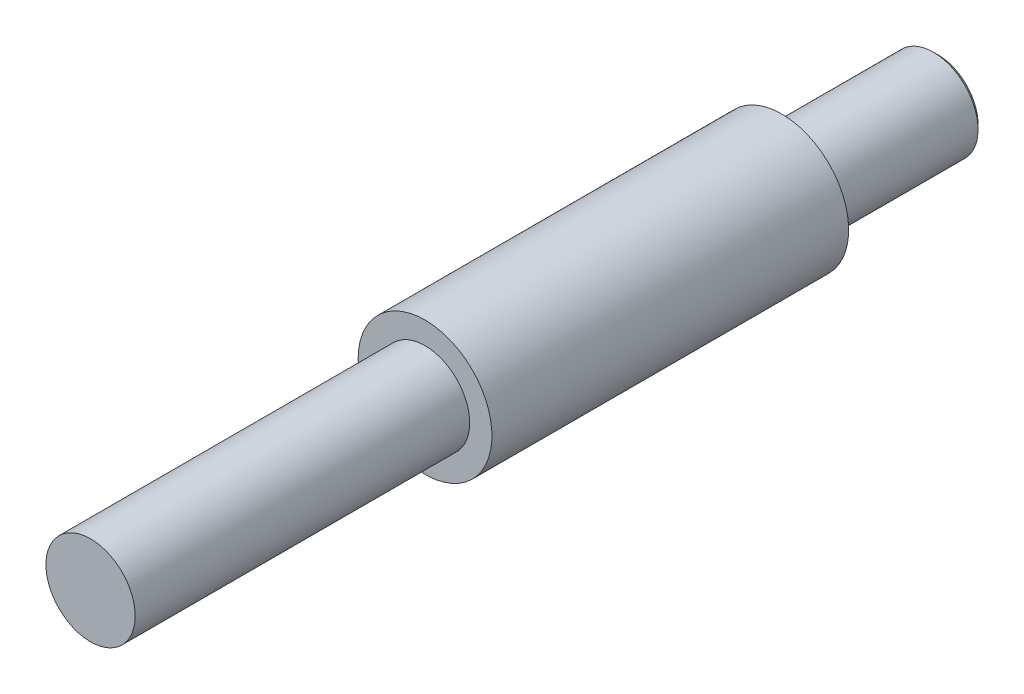
SolidWorks part; units mm, degrees
ref_plane "Front Plane" through (0, 0, 0) normal (0, 0, 1) x (1, 0, 0)
ref_plane "Top Plane" through (0, 0, 0) normal (0, 1, 0) x (1, 0, 0)
ref_plane "Right Plane" through (0, 0, 0) normal (1, 0, 0) x (0, 0, -1)
sketch "Sketch1" plane through (0, 0, 0) normal (0, 0, 1) x (1, 0, 0)
  circle A0 centre (0, 0) radius 10.01
  dimension "D1" = 20.02
extrude "Boss-Extrude1" add sketch "Sketch1" against normal blind 75
sketch "Sketch2" plane through (0, 0, -75) normal (0, 0, -1) x (-1, 0, 0)
  circle A0 centre (0, 0) radius 15
  dimension "D1" = 30
extrude "Boss-Extrude2" add sketch "Sketch2" along normal blind 80
sketch "Sketch3" plane through (0, 0, -155) normal (0, 0, -1) x (-1, 0, 0)
  circle A0 centre (0, 0) radius 10.01
  dimension "D1" = 20.02
extrude "Boss-Extrude3" add sketch "Sketch3" along normal blind 35
chamfer "Chamfer1" distance 1 angle 45 1 edges at (-10.01, 0, -190)
